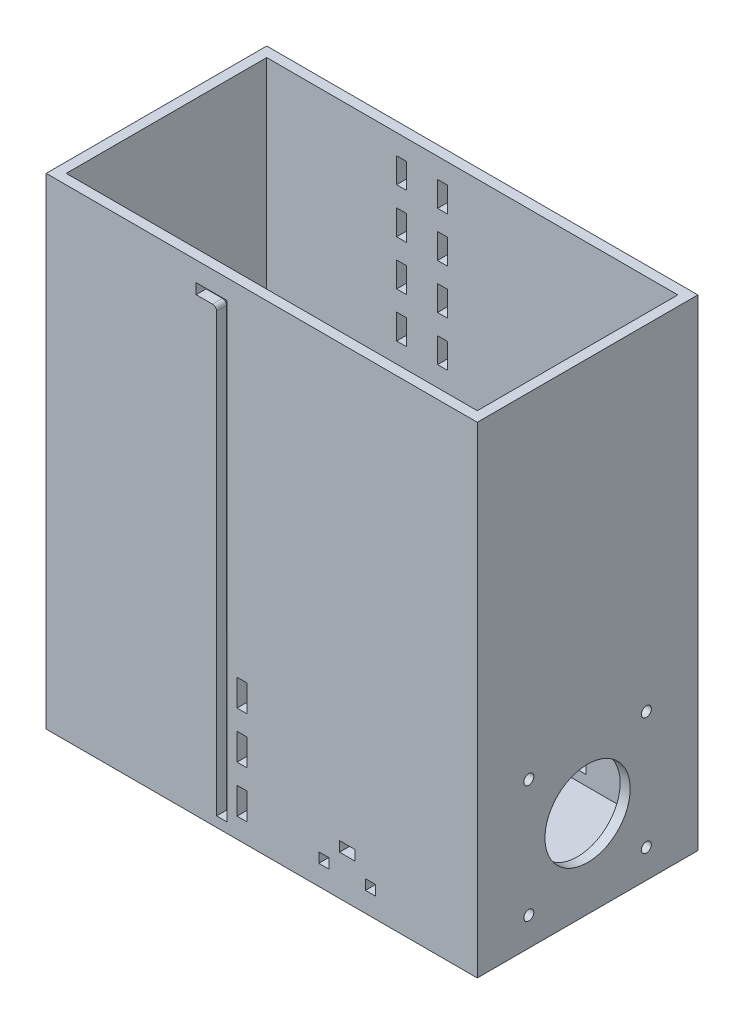
SolidWorks part; units mm, degrees
material "Acrylic (Medium-high impact)"
ref_plane "Front Plane" through (0, 0, 0) normal (0, 0, 1) x (1, 0, 0)
ref_plane "Top Plane" through (0, 0, 0) normal (0, 1, 0) x (1, 0, 0)
ref_plane "Right Plane" through (0, 0, 0) normal (1, 0, 0) x (0, 0, -1)
sketch "Sketch1" plane through (0, 0, 0) normal (0, 1, 0) x (1, 0, 0)
  line L1 (-136.525, 69.85) -> (136.525, 69.85)
  line L2 (-136.525, 69.85) -> (-136.525, -69.85)
  line L3 (-136.525, -69.85) -> (136.525, -69.85)
  line L4 (136.525, 69.85) -> (136.525, -69.85)
  point P4 (-136.525, 0)
  point P6 (0, 69.85)
  dimension "D1" = 139.7
  dimension "D2" = 273.05
extrude "Boss-Extrude1" add sketch "Sketch1" along normal blind 6.35
sketch "Sketch2" plane through (0, 6.35, 0) normal (0, 1, 0) x (1, 0, 0)
  line L0 (136.525, -69.85) -> (136.525, 69.85) construction
  line L1 (-136.525, 69.85) -> (136.525, 69.85)
  line L2 (-136.525, 69.85) -> (-136.525, -69.85)
  line L3 (-136.525, -69.85) -> (136.525, -69.85)
  line L4 (136.525, 69.85) -> (136.525, -69.85)
  line L5 (-136.525, -69.85) -> (136.525, -69.85) construction
  line L7 (-130.175, 63.5) -> (130.175, 63.5)
  line L8 (-130.175, 63.5) -> (-130.175, -63.5)
  line L9 (-130.175, -63.5) -> (130.175, -63.5)
  line L10 (130.175, 63.5) -> (130.175, -63.5)
  point P7 (-130.175, 0)
  point P14 (-136.525, 0)
  point P15 (0, -63.5)
  point P16 (0, -69.85)
  point P17 (130.175, 0)
  point P18 (136.525, 0)
  dimension "D1" = 6.35
  dimension "D2" = 6.35
extrude "Boss-Extrude2" add sketch "Sketch2" along normal blind 298.45
sketch "Sketch3" plane through (0, 0, 69.85) normal (0, 0, 1) x (1, 0, 0)
  line L0 (-25.273, 304.8) -> (-25.273, 0) construction
  line L2 (-130.175, 6.35) -> (130.175, 6.35) construction
  line L4 (-28.575, 283.21) -> (-28.575, 6.35)
  line L5 (-28.575, 6.35) -> (-21.971, 6.35)
  line L6 (-21.971, 292.354) -> (-21.971, 6.35)
  line L7 (-21.971, 292.354) -> (-41.529, 292.354)
  line L9 (-31.115, 285.75) -> (-41.529, 285.75)
  line L10 (-41.529, 292.354) -> (-41.529, 285.75)
  line L11 (-21.971, 101.6) -> (-9.271, 101.6) construction
  line L12 (-136.525, 0) -> (136.525, 0) construction
  line L13 (-12.446, 88.9) -> (-12.446, 101.6) construction
  line L14 (-15.621, 88.9) -> (-9.271, 88.9)
  line L15 (-15.621, 88.9) -> (-15.621, 71.9667)
  line L16 (-15.621, 71.9667) -> (-9.271, 71.9667)
  line L17 (-9.271, 88.9) -> (-9.271, 71.9667)
  line L18 (-15.621, 42.3333) -> (-9.271, 42.3333)
  line L19 (-15.621, 42.3333) -> (-15.621, 59.2667)
  line L20 (-15.621, 59.2667) -> (-9.271, 59.2667)
  line L21 (-9.271, 42.3333) -> (-9.271, 59.2667)
  line L26 (-15.621, 29.6333) -> (-9.271, 29.6333)
  line L27 (-15.621, 29.6333) -> (-15.621, 12.7)
  line L28 (-15.621, 12.7) -> (-9.271, 12.7)
  line L29 (-9.271, 29.6333) -> (-9.271, 12.7)
  line L30 (-12.446, 59.2667) -> (-12.446, 71.9667) construction
  line L31 (-12.446, 29.6333) -> (-12.446, 42.3333) construction
  line L32 (-12.446, 12.7) -> (-12.446, 0) construction
  line L33 (-136.525, 304.8) -> (136.525, 304.8) construction
  line L34 (-130.175, 304.8) -> (-130.175, 6.35) construction
  arc A0 (-28.575, 283.21) -> (-31.115, 285.75) centre (-31.115, 283.21) ccw
  point P2 (-65.1597, 304.8)
  point P5 (-25.273, 6.35)
  point P40 (0, 0)
  point P41 (0, 0)
  point P42 (0, 0)
  point P44 (-65.2242, 0)
  point P45 (-69.6985, 0)
  dimension "D5" = 2.54
  dimension "D1" = 6.604
  dimension "D2" = 12.954
  dimension "D3" = 6.604
  dimension "D4" = 286.004
  dimension "D6" = 101.6
  dimension "D7" = 12.7
  dimension "D8" = 12.7
  dimension "D9" = 6.35
  dimension "D10" = 101.6
extrude "Door Slot" cut sketch "Sketch3" against normal blind 12.7
sketch "Sketch4" plane through (0, 0, -63.5) normal (0, 0, 1) x (1, 0, 0)
  line L0 (-136.525, 304.8) -> (136.525, 304.8) construction
  line L1 (-47.879, 304.8) -> (-41.529, 304.8)
  line L2 (-47.879, 304.8) -> (-47.879, 6.35)
  line L3 (-47.879, 6.35) -> (-41.529, 6.35)
  line L4 (-41.529, 304.8) -> (-41.529, 6.35)
  line L5 (-18.796, 263.525) -> (-18.796, 247.65) construction
  line L6 (-41.529, 292.354) -> (-41.529, 285.75) construction
  line L7 (-21.971, 304.8) -> (-15.621, 304.8)
  line L8 (-21.971, 304.8) -> (-21.971, 6.35)
  line L9 (-21.971, 6.35) -> (-15.621, 6.35)
  line L10 (-15.621, 304.8) -> (-15.621, 6.35)
  line L11 (130.175, 6.35) -> (-130.175, 6.35) construction
  line L12 (-21.971, 6.35) -> (-21.971, 292.354) construction
  line L13 (-41.529, 304.8) -> (-47.879, 304.8)
  line L14 (-41.529, 304.8) -> (-41.529, 292.1)
  line L15 (-41.529, 292.1) -> (-47.879, 292.1)
  line L16 (-47.879, 304.8) -> (-47.879, 292.1)
  line L17 (-41.529, 276.225) -> (-47.879, 276.225)
  line L18 (-41.529, 276.225) -> (-41.529, 263.525)
  line L19 (-41.529, 263.525) -> (-47.879, 263.525)
  line L20 (-47.879, 276.225) -> (-47.879, 263.525)
  line L21 (-47.879, 6.35) -> (-41.529, 6.35)
  line L22 (-47.879, 6.35) -> (-47.879, 19.05)
  line L23 (-47.879, 19.05) -> (-41.529, 19.05)
  line L24 (-41.529, 6.35) -> (-41.529, 19.05)
  line L25 (-47.879, 34.925) -> (-41.529, 34.925)
  line L26 (-47.879, 34.925) -> (-47.879, 47.625)
  line L27 (-47.879, 47.625) -> (-41.529, 47.625)
  line L28 (-41.529, 34.925) -> (-41.529, 47.625)
  line L29 (-47.879, 92.075) -> (-41.529, 92.075)
  line L30 (-47.879, 92.075) -> (-47.879, 104.775)
  line L31 (-47.879, 104.775) -> (-41.529, 104.775)
  line L32 (-41.529, 92.075) -> (-41.529, 104.775)
  line L33 (-47.879, 149.225) -> (-41.529, 149.225)
  line L34 (-47.879, 149.225) -> (-47.879, 161.925)
  line L35 (-47.879, 161.925) -> (-41.529, 161.925)
  line L36 (-41.529, 149.225) -> (-41.529, 161.925)
  line L37 (-47.879, 177.8) -> (-41.529, 177.8)
  line L38 (-47.879, 177.8) -> (-47.879, 190.5)
  line L39 (-47.879, 190.5) -> (-41.529, 190.5)
  line L40 (-41.529, 177.8) -> (-41.529, 190.5)
  line L41 (-47.879, 206.375) -> (-41.529, 206.375)
  line L42 (-47.879, 206.375) -> (-47.879, 219.075)
  line L43 (-47.879, 219.075) -> (-41.529, 219.075)
  line L44 (-41.529, 206.375) -> (-41.529, 219.075)
  line L45 (-47.879, 234.95) -> (-41.529, 234.95)
  line L46 (-47.879, 234.95) -> (-47.879, 247.65)
  line L47 (-47.879, 247.65) -> (-41.529, 247.65)
  line L48 (-41.529, 234.95) -> (-41.529, 247.65)
  line L49 (-41.529, 133.35) -> (-47.879, 133.35)
  line L50 (-41.529, 133.35) -> (-41.529, 120.65)
  line L51 (-41.529, 120.65) -> (-47.879, 120.65)
  line L52 (-47.879, 133.35) -> (-47.879, 120.65)
  line L53 (-41.529, 76.2) -> (-47.879, 76.2)
  line L54 (-41.529, 76.2) -> (-41.529, 63.5)
  line L55 (-41.529, 63.5) -> (-47.879, 63.5)
  line L56 (-47.879, 76.2) -> (-47.879, 63.5)
  line L57 (-44.704, 304.8) -> (-44.704, 292.1) construction
  line L58 (-44.704, 292.1) -> (-44.704, 276.225) construction
  line L59 (-44.704, 276.225) -> (-44.704, 263.525) construction
  line L60 (-44.704, 247.65) -> (-44.704, 234.95) construction
  line L61 (-44.704, 234.95) -> (-44.704, 219.075) construction
  line L62 (-44.704, 219.075) -> (-44.704, 206.375) construction
  line L63 (-44.704, 206.375) -> (-44.704, 190.5) construction
  line L64 (-44.704, 190.5) -> (-44.704, 177.8) construction
  line L65 (-44.704, 177.8) -> (-44.704, 161.925) construction
  line L66 (-44.704, 161.925) -> (-44.704, 149.225) construction
  line L67 (-44.704, 133.35) -> (-44.704, 120.65) construction
  line L68 (-44.704, 120.65) -> (-44.704, 104.775) construction
  line L69 (-44.704, 104.775) -> (-44.704, 92.075) construction
  line L70 (-44.704, 92.075) -> (-44.704, 76.2) construction
  line L71 (-44.704, 76.2) -> (-44.704, 63.5) construction
  line L72 (-44.704, 63.5) -> (-44.704, 47.625) construction
  line L73 (-44.704, 47.625) -> (-44.704, 34.925) construction
  line L74 (-44.704, 34.925) -> (-44.704, 19.05) construction
  line L75 (-44.704, 19.05) -> (-44.704, 6.35) construction
  line L76 (-44.704, 149.225) -> (-44.704, 133.35) construction
  line L77 (-44.704, 263.525) -> (-44.704, 247.65) construction
  line L78 (-31.75, 304.8) -> (-31.75, 0) construction
  line L79 (136.525, 304.8) -> (-136.525, 304.8) construction
  line L80 (136.525, 0) -> (-136.525, 0) construction
  line L81 (-31.75, 8.3493) -> (-21.971, 8.3493) construction
  line L82 (-31.75, 8.3493) -> (-41.529, 8.3493) construction
  line L83 (-18.796, 149.225) -> (-18.796, 133.35) construction
  line L84 (-18.796, 19.05) -> (-18.796, 6.35) construction
  line L85 (-18.796, 34.925) -> (-18.796, 19.05) construction
  line L86 (-18.796, 47.625) -> (-18.796, 34.925) construction
  line L87 (-18.796, 63.5) -> (-18.796, 47.625) construction
  line L88 (-18.796, 76.2) -> (-18.796, 63.5) construction
  line L89 (-18.796, 92.075) -> (-18.796, 76.2) construction
  line L90 (-18.796, 104.775) -> (-18.796, 92.075) construction
  line L91 (-18.796, 120.65) -> (-18.796, 104.775) construction
  line L92 (-18.796, 133.35) -> (-18.796, 120.65) construction
  line L93 (-18.796, 161.925) -> (-18.796, 149.225) construction
  line L94 (-18.796, 177.8) -> (-18.796, 161.925) construction
  line L95 (-18.796, 190.5) -> (-18.796, 177.8) construction
  line L96 (-18.796, 206.375) -> (-18.796, 190.5) construction
  line L97 (-18.796, 219.075) -> (-18.796, 206.375) construction
  line L98 (-18.796, 234.95) -> (-18.796, 219.075) construction
  line L99 (-18.796, 247.65) -> (-18.796, 234.95) construction
  line L100 (-18.796, 276.225) -> (-18.796, 263.525) construction
  line L101 (-18.796, 292.1) -> (-18.796, 276.225) construction
  line L102 (-18.796, 304.8) -> (-18.796, 292.1) construction
  line L103 (-15.621, 76.2) -> (-15.621, 63.5)
  line L104 (-21.971, 63.5) -> (-15.621, 63.5)
  line L105 (-21.971, 76.2) -> (-21.971, 63.5)
  line L106 (-21.971, 76.2) -> (-15.621, 76.2)
  line L107 (-15.621, 133.35) -> (-15.621, 120.65)
  line L108 (-21.971, 120.65) -> (-15.621, 120.65)
  line L109 (-21.971, 133.35) -> (-21.971, 120.65)
  line L110 (-21.971, 133.35) -> (-15.621, 133.35)
  line L111 (-21.971, 234.95) -> (-21.971, 247.65)
  line L112 (-15.621, 247.65) -> (-21.971, 247.65)
  line L113 (-15.621, 234.95) -> (-15.621, 247.65)
  line L114 (-15.621, 234.95) -> (-21.971, 234.95)
  line L115 (-21.971, 206.375) -> (-21.971, 219.075)
  line L116 (-15.621, 219.075) -> (-21.971, 219.075)
  line L117 (-15.621, 206.375) -> (-15.621, 219.075)
  line L118 (-15.621, 206.375) -> (-21.971, 206.375)
  line L119 (-21.971, 177.8) -> (-21.971, 190.5)
  line L120 (-15.621, 190.5) -> (-21.971, 190.5)
  line L121 (-15.621, 177.8) -> (-15.621, 190.5)
  line L122 (-15.621, 177.8) -> (-21.971, 177.8)
  line L123 (-21.971, 149.225) -> (-21.971, 161.925)
  line L124 (-15.621, 161.925) -> (-21.971, 161.925)
  line L125 (-15.621, 149.225) -> (-15.621, 161.925)
  line L126 (-15.621, 149.225) -> (-21.971, 149.225)
  line L127 (-21.971, 92.075) -> (-21.971, 104.775)
  line L128 (-15.621, 104.775) -> (-21.971, 104.775)
  line L129 (-15.621, 92.075) -> (-15.621, 104.775)
  line L130 (-15.621, 92.075) -> (-21.971, 92.075)
  line L131 (-21.971, 34.925) -> (-21.971, 47.625)
  line L132 (-15.621, 47.625) -> (-21.971, 47.625)
  line L133 (-15.621, 34.925) -> (-15.621, 47.625)
  line L134 (-15.621, 34.925) -> (-21.971, 34.925)
  line L135 (-21.971, 6.35) -> (-21.971, 19.05)
  line L136 (-15.621, 19.05) -> (-21.971, 19.05)
  line L137 (-15.621, 6.35) -> (-15.621, 19.05)
  line L138 (-15.621, 6.35) -> (-21.971, 6.35)
  line L139 (-15.621, 276.225) -> (-15.621, 263.525)
  line L140 (-21.971, 263.525) -> (-15.621, 263.525)
  line L141 (-21.971, 276.225) -> (-21.971, 263.525)
  line L142 (-21.971, 276.225) -> (-15.621, 276.225)
  line L143 (-15.621, 304.8) -> (-15.621, 292.1)
  line L144 (-21.971, 292.1) -> (-15.621, 292.1)
  line L145 (-21.971, 304.8) -> (-21.971, 292.1)
  line L146 (-21.971, 304.8) -> (-15.621, 304.8)
  line L147 (-21.971, 304.8) -> (-21.971, 6.35)
  line L148 (-15.621, 6.35) -> (-21.971, 6.35)
  line L149 (-15.621, 304.8) -> (-15.621, 6.35)
  line L150 (-15.621, 304.8) -> (-21.971, 304.8)
  point P14 (-41.529, 289.052)
  dimension "D1" = 6.35
  dimension "D2" = 12.7
extrude "Door Guide Holes" cut sketch "Sketch4" against normal up to next contours L17 L4 L15 L2 | L2 L47 L4 L19 | L45 L2 L43 L4 | L41 L2 L39 L4 | L37 L2 L35 L4 | L49 L4 L33 L2 | L4 L51 L2 L31 | L53 L4 L29 L2 | L4 L55 L2 L27 | L25 L2 L23 L4
ref_plane "Plane1" through (-31.75, 0, 0) normal (-1, 0, 0) x (0, 0, 1)
mirror "Mirror1" about plane through (-31.75, 0, 0) normal (-1, 0, 0) of "Door Guide Holes"
sketch "Lever Holes" plane through (0, 0, 69.85) normal (0, 0, 1) x (1, 0, 0)
  line L0 (49.276, 31.75) -> (58.928, 31.75)
  line L1 (49.276, 31.75) -> (49.276, 25.4)
  line L2 (49.276, 25.4) -> (58.928, 25.4)
  line L3 (58.928, 31.75) -> (58.928, 25.4)
  line L4 (36.1315, 19.05) -> (42.4815, 19.05)
  line L5 (36.1315, 19.05) -> (36.1315, 12.7)
  line L6 (36.1315, 12.7) -> (42.4815, 12.7)
  line L7 (42.4815, 19.05) -> (42.4815, 12.7)
  line L8 (65.7225, 19.05) -> (72.0725, 19.05)
  line L9 (65.7225, 19.05) -> (65.7225, 12.7)
  line L10 (65.7225, 12.7) -> (72.0725, 12.7)
  line L11 (72.0725, 19.05) -> (72.0725, 12.7)
  line L12 (42.4815, 15.875) -> (65.7225, 15.875) construction
  line L13 (-136.525, 0) -> (136.525, 0) construction
  line L14 (-21.971, 6.35) -> (130.175, 6.35) construction
  line L15 (130.175, 6.35) -> (-130.175, 6.35) construction
  point P12 (54.102, 15.875)
  point P13 (54.102, 25.4)
  point P14 (39.3065, 12.7)
  point P24 (54.102, 6.35)
  point P25 (0, 0)
  dimension "D1" = 9.652
  dimension "D2" = 6.35
  dimension "D3" = 6.35
  dimension "D4" = 6.35
  dimension "D5" = 23.241
  dimension "D6" = 25.4
  dimension "D7" = 12.7
extrude "Cut-Extrude1" cut sketch "Lever Holes" against normal through all
sketch "Sketch7" plane through (136.525, 0, 0) normal (1, 0, 0) x (0, 0, -1)
  line L0 (-37.211, 92.583) -> (37.211, 92.583)
  line L1 (-37.211, 92.583) -> (-37.211, 18.161)
  line L2 (-37.211, 18.161) -> (37.211, 18.161)
  line L3 (37.211, 92.583) -> (37.211, 18.161)
  line L4 (-69.85, 0) -> (69.85, 0) construction
  circle A0 centre (0, 55.372) radius 26.9875
  circle A1 centre (-37.211, 92.583) radius 3.175
  circle A2 centre (37.211, 92.583) radius 3.175
  circle A3 centre (-37.211, 18.161) radius 3.175
  circle A4 centre (37.211, 18.161) radius 3.175
  point P9 (0, 18.161)
  point P10 (-37.211, 55.372)
  point P12 (43.7877, 25.7461)
  point P15 (0, 0)
  dimension "D3" = 53.975
  dimension "D4" = 6.35
  dimension "D1" = 74.422
  dimension "D2" = 55.372
extrude "Cut-Extrude2" cut sketch "Sketch7" against normal up to next contours A0 | L0 A1 L1 | L1 A1 L0 | L3 A2 L0 | L0 A2 L3 | L2 A3 L1 | L1 A3 L2 | L2 A4 L3 | L3 A4 L2
sketch "Sketch8" plane through (-136.525, 0, 0) normal (-1, 0, 0) x (0, 0, 1)
  line L0 (-69.85, 0) -> (69.85, 0) construction
  circle A0 centre (0, 19.05) radius 3.175
  point P2 (0, 0)
  point P6 (0, 0)
  dimension "D1" = 6.35
  dimension "D2" = 19.05
extrude "Cut-Extrude3" cut sketch "Sketch8" against normal up to next
sketch "Bottom" plane through (0, 0, 0) normal (0, -1, 0) x (1, 0, 0)
  line L0 (-130.175, 63.5) -> (130.175, 63.5) construction
  line L1 (-136.525, 69.85) -> (-122.1539, 69.85)
  line L2 (-136.525, 69.85) -> (-136.525, 63.5)
  line L3 (-136.525, 63.5) -> (-122.1539, 63.5)
  line L4 (-122.1539, 69.85) -> (-122.1539, 63.5)
  line L5 (-122.1539, 69.85) -> (-107.7829, 69.85)
  line L6 (-122.1539, 69.85) -> (-122.1539, 63.5)
  line L7 (-122.1539, 63.5) -> (-107.7829, 63.5)
  line L8 (-107.7829, 69.85) -> (-107.7829, 63.5)
  line L9 (-107.7829, 69.85) -> (-93.4118, 69.85)
  line L10 (-107.7829, 69.85) -> (-107.7829, 63.5)
  line L11 (-107.7829, 63.5) -> (-93.4118, 63.5)
  line L12 (-93.4118, 69.85) -> (-93.4118, 63.5)
  line L13 (-93.4118, 69.85) -> (-79.0408, 69.85)
  line L14 (-93.4118, 69.85) -> (-93.4118, 63.5)
  line L15 (-93.4118, 63.5) -> (-79.0408, 63.5)
  line L16 (-79.0408, 69.85) -> (-79.0408, 63.5)
  line L17 (-136.525, 69.85) -> (136.525, 69.85) construction
  line L18 (-41.529, 63.5) -> (-21.971, 63.5) construction
  line L19 (-79.0408, 69.85) -> (-64.6697, 69.85)
  line L20 (-79.0408, 69.85) -> (-79.0408, 63.5)
  line L21 (-79.0408, 63.5) -> (-64.6697, 63.5)
  line L22 (-64.6697, 69.85) -> (-64.6697, 63.5)
  line L23 (-64.6697, 69.85) -> (-50.2987, 69.85)
  line L24 (-64.6697, 69.85) -> (-64.6697, 63.5)
  line L25 (-64.6697, 63.5) -> (-50.2987, 63.5)
  line L26 (-50.2987, 69.85) -> (-50.2987, 63.5)
  line L27 (-50.2987, 69.85) -> (-35.9276, 69.85)
  line L28 (-50.2987, 69.85) -> (-50.2987, 63.5)
  line L29 (-50.2987, 63.5) -> (-35.9276, 63.5)
  line L30 (-35.9276, 69.85) -> (-35.9276, 63.5)
  line L31 (-35.9276, 69.85) -> (-21.5566, 69.85)
  line L32 (-35.9276, 69.85) -> (-35.9276, 63.5)
  line L33 (-35.9276, 63.5) -> (-21.5566, 63.5)
  line L34 (-21.5566, 69.85) -> (-21.5566, 63.5)
  line L36 (-21.5566, 69.85) -> (-7.1855, 69.85)
  line L37 (-21.5566, 69.85) -> (-21.5566, 63.5)
  line L38 (-21.5566, 63.5) -> (-7.1855, 63.5)
  line L39 (-7.1855, 69.85) -> (-7.1855, 63.5)
  line L40 (-7.1855, 69.85) -> (7.1855, 69.85)
  line L41 (-7.1855, 69.85) -> (-7.1855, 63.5)
  line L42 (-7.1855, 63.5) -> (7.1855, 63.5)
  line L43 (7.1855, 69.85) -> (7.1855, 63.5)
  line L44 (7.1855, 69.85) -> (21.5566, 69.85)
  line L45 (7.1855, 69.85) -> (7.1855, 63.5)
  line L46 (7.1855, 63.5) -> (21.5566, 63.5)
  line L47 (21.5566, 69.85) -> (21.5566, 63.5)
  line L48 (21.5566, 69.85) -> (35.9276, 69.85)
  line L49 (21.5566, 69.85) -> (21.5566, 63.5)
  line L50 (21.5566, 63.5) -> (35.9276, 63.5)
  line L51 (35.9276, 69.85) -> (35.9276, 63.5)
  line L52 (35.9276, 69.85) -> (50.2987, 69.85)
  line L53 (35.9276, 69.85) -> (35.9276, 63.5)
  line L54 (35.9276, 63.5) -> (50.2987, 63.5)
  line L55 (50.2987, 69.85) -> (50.2987, 63.5)
  line L56 (50.2987, 69.85) -> (64.6697, 69.85)
  line L57 (50.2987, 69.85) -> (50.2987, 63.5)
  line L58 (50.2987, 63.5) -> (64.6697, 63.5)
  line L59 (64.6697, 69.85) -> (64.6697, 63.5)
  line L60 (64.6697, 69.85) -> (79.0408, 69.85)
  line L61 (64.6697, 69.85) -> (64.6697, 63.5)
  line L62 (64.6697, 63.5) -> (79.0408, 63.5)
  line L63 (79.0408, 69.85) -> (79.0408, 63.5)
  line L64 (79.0408, 69.85) -> (93.4118, 69.85)
  line L65 (79.0408, 69.85) -> (79.0408, 63.5)
  line L66 (79.0408, 63.5) -> (93.4118, 63.5)
  line L67 (93.4118, 69.85) -> (93.4118, 63.5)
  line L68 (93.4118, 69.85) -> (107.7829, 69.85)
  line L69 (93.4118, 69.85) -> (93.4118, 63.5)
  line L70 (93.4118, 63.5) -> (107.7829, 63.5)
  line L71 (107.7829, 69.85) -> (107.7829, 63.5)
  line L72 (107.7829, 69.85) -> (122.1539, 69.85)
  line L73 (107.7829, 69.85) -> (107.7829, 63.5)
  line L74 (107.7829, 63.5) -> (122.1539, 63.5)
  line L75 (122.1539, 69.85) -> (122.1539, 63.5)
  line L76 (-130.175, -63.5) -> (-130.175, 63.5) construction
  line L77 (-136.525, 69.85) -> (-130.175, 69.85)
  line L78 (-136.525, 69.85) -> (-136.525, 57.15)
  line L79 (-136.525, 57.15) -> (-130.175, 57.15)
  line L80 (-130.175, 69.85) -> (-130.175, 57.15)
  line L82 (-136.525, 57.15) -> (-130.175, 57.15)
  line L83 (-136.525, 57.15) -> (-136.525, 44.45)
  line L84 (-136.525, 44.45) -> (-130.175, 44.45)
  line L85 (-130.175, 57.15) -> (-130.175, 44.45)
  line L86 (-136.525, 44.45) -> (-130.175, 44.45)
  line L87 (-136.525, 44.45) -> (-136.525, 31.75)
  line L88 (-136.525, 31.75) -> (-130.175, 31.75)
  line L89 (-130.175, 44.45) -> (-130.175, 31.75)
  line L90 (-136.525, 31.75) -> (-130.175, 31.75)
  line L91 (-136.525, 31.75) -> (-136.525, 19.05)
  line L92 (-136.525, 19.05) -> (-130.175, 19.05)
  line L93 (-130.175, 31.75) -> (-130.175, 19.05)
  line L94 (-136.525, 19.05) -> (-130.175, 19.05)
  line L95 (-136.525, 19.05) -> (-136.525, 6.35)
  line L96 (-136.525, 6.35) -> (-130.175, 6.35)
  line L97 (-130.175, 19.05) -> (-130.175, 6.35)
  line L98 (-136.525, 6.35) -> (-130.175, 6.35)
  line L99 (-136.525, 6.35) -> (-136.525, -6.35)
  line L100 (-136.525, -6.35) -> (-130.175, -6.35)
  line L101 (-130.175, 6.35) -> (-130.175, -6.35)
  line L102 (-136.525, -6.35) -> (-130.175, -6.35)
  line L103 (-136.525, -6.35) -> (-136.525, -19.05)
  line L104 (-136.525, -19.05) -> (-130.175, -19.05)
  line L105 (-130.175, -6.35) -> (-130.175, -19.05)
  line L106 (-136.525, -19.05) -> (-130.175, -19.05)
  line L107 (-136.525, -19.05) -> (-136.525, -31.75)
  line L108 (-136.525, -31.75) -> (-130.175, -31.75)
  line L109 (-130.175, -19.05) -> (-130.175, -31.75)
  line L110 (-136.525, -31.75) -> (-130.175, -31.75)
  line L111 (-136.525, -31.75) -> (-136.525, -44.45)
  line L112 (-136.525, -44.45) -> (-130.175, -44.45)
  line L113 (-130.175, -31.75) -> (-130.175, -44.45)
  line L114 (-136.525, -44.45) -> (-130.175, -44.45)
  line L115 (-136.525, -44.45) -> (-136.525, -57.15)
  line L116 (-136.525, -57.15) -> (-130.175, -57.15)
  line L117 (-130.175, -44.45) -> (-130.175, -57.15)
  line L118 (136.525, 69.85) -> (136.525, -69.85) construction
  line L119 (122.1539, 69.85) -> (136.525, 69.85)
  line L120 (122.1539, 69.85) -> (122.1539, 63.5)
  line L121 (122.1539, 63.5) -> (136.525, 63.5)
  line L122 (136.525, 69.85) -> (136.525, 63.5)
  line L123 (136.525, -69.85) -> (-136.525, -69.85) construction
  line L124 (-136.525, -57.15) -> (-130.175, -57.15)
  line L125 (-136.525, -57.15) -> (-136.525, -69.85)
  line L126 (-136.525, -69.85) -> (-130.175, -69.85)
  line L127 (-130.175, -57.15) -> (-130.175, -69.85)
  line L128 (150.1775, 0) -> (-150.1775, 0) construction
  line L129 (136.525, -69.85) -> (136.525, -63.5)
  line L130 (122.1539, -63.5) -> (136.525, -63.5)
  line L131 (122.1539, -69.85) -> (136.525, -69.85)
  line L132 (122.1539, -69.85) -> (122.1539, -63.5)
  line L133 (107.7829, -63.5) -> (122.1539, -63.5)
  line L134 (107.7829, -69.85) -> (122.1539, -69.85)
  line L135 (107.7829, -69.85) -> (107.7829, -63.5)
  line L136 (93.4118, -63.5) -> (107.7829, -63.5)
  line L137 (93.4118, -69.85) -> (107.7829, -69.85)
  line L138 (93.4118, -69.85) -> (93.4118, -63.5)
  line L139 (79.0408, -63.5) -> (93.4118, -63.5)
  line L140 (79.0408, -69.85) -> (93.4118, -69.85)
  line L141 (79.0408, -69.85) -> (79.0408, -63.5)
  line L142 (64.6697, -63.5) -> (79.0408, -63.5)
  line L143 (64.6697, -69.85) -> (79.0408, -69.85)
  line L144 (50.2987, -63.5) -> (64.6697, -63.5)
  line L145 (64.6697, -69.85) -> (64.6697, -63.5)
  line L146 (50.2987, -69.85) -> (64.6697, -69.85)
  line L147 (50.2987, -69.85) -> (50.2987, -63.5)
  line L148 (35.9276, -63.5) -> (50.2987, -63.5)
  line L149 (35.9276, -69.85) -> (50.2987, -69.85)
  line L150 (35.9276, -69.85) -> (35.9276, -63.5)
  line L151 (21.5566, -63.5) -> (35.9276, -63.5)
  line L152 (21.5566, -69.85) -> (35.9276, -69.85)
  line L153 (21.5566, -69.85) -> (21.5566, -63.5)
  line L154 (7.1855, -69.85) -> (21.5566, -69.85)
  line L155 (7.1855, -63.5) -> (21.5566, -63.5)
  line L156 (7.1855, -69.85) -> (7.1855, -63.5)
  line L157 (-7.1855, -63.5) -> (7.1855, -63.5)
  line L158 (-7.1855, -69.85) -> (7.1855, -69.85)
  line L159 (-21.5566, -63.5) -> (-7.1855, -63.5)
  line L160 (-7.1855, -69.85) -> (-7.1855, -63.5)
  line L161 (-21.5566, -69.85) -> (-7.1855, -69.85)
  line L162 (-21.5566, -69.85) -> (-21.5566, -63.5)
  line L163 (-35.9276, -63.5) -> (-21.5566, -63.5)
  line L164 (-35.9276, -69.85) -> (-21.5566, -69.85)
  line L165 (-35.9276, -69.85) -> (-35.9276, -63.5)
  line L166 (-50.2987, -63.5) -> (-35.9276, -63.5)
  line L167 (-50.2987, -69.85) -> (-35.9276, -69.85)
  line L168 (-50.2987, -69.85) -> (-50.2987, -63.5)
  line L169 (-64.6697, -69.85) -> (-50.2987, -69.85)
  line L170 (-64.6697, -63.5) -> (-50.2987, -63.5)
  line L171 (-79.0408, -63.5) -> (-64.6697, -63.5)
  line L172 (-64.6697, -69.85) -> (-64.6697, -63.5)
  line L173 (-79.0408, -69.85) -> (-64.6697, -69.85)
  line L174 (-93.4118, -69.85) -> (-79.0408, -69.85)
  line L175 (-93.4118, -63.5) -> (-79.0408, -63.5)
  line L176 (-79.0408, -69.85) -> (-79.0408, -63.5)
  line L177 (-107.7829, -69.85) -> (-107.7829, -63.5)
  line L178 (-107.7829, -69.85) -> (-93.4118, -69.85)
  line L179 (-93.4118, -69.85) -> (-93.4118, -63.5)
  line L180 (-107.7829, -63.5) -> (-93.4118, -63.5)
  line L181 (-122.1539, -63.5) -> (-107.7829, -63.5)
  line L182 (-122.1539, -69.85) -> (-107.7829, -69.85)
  line L183 (-122.1539, -69.85) -> (-122.1539, -63.5)
  line L184 (-136.525, -69.85) -> (-122.1539, -69.85)
  line L185 (-136.525, -69.85) -> (-136.525, -63.5)
  line L186 (-136.525, -63.5) -> (-122.1539, -63.5)
  line L187 (0, -76.835) -> (0, 76.835) construction
  line L188 (136.525, -69.85) -> (130.175, -69.85)
  line L189 (130.175, -57.15) -> (130.175, -69.85)
  line L190 (136.525, -57.15) -> (136.525, -69.85)
  line L191 (136.525, -57.15) -> (130.175, -57.15)
  line L192 (130.175, -44.45) -> (130.175, -57.15)
  line L193 (136.525, -44.45) -> (136.525, -57.15)
  line L194 (136.525, -44.45) -> (130.175, -44.45)
  line L195 (130.175, -31.75) -> (130.175, -44.45)
  line L196 (136.525, -31.75) -> (136.525, -44.45)
  line L197 (136.525, -31.75) -> (130.175, -31.75)
  line L198 (136.525, -19.05) -> (136.525, -31.75)
  line L199 (130.175, -19.05) -> (130.175, -31.75)
  line L200 (130.175, -6.35) -> (130.175, -19.05)
  line L201 (136.525, -6.35) -> (136.525, -19.05)
  line L202 (136.525, -19.05) -> (130.175, -19.05)
  line L203 (136.525, -6.35) -> (130.175, -6.35)
  line L204 (130.175, 6.35) -> (130.175, -6.35)
  line L205 (136.525, 6.35) -> (136.525, -6.35)
  line L206 (136.525, 6.35) -> (130.175, 6.35)
  line L207 (130.175, 19.05) -> (130.175, 6.35)
  line L208 (136.525, 19.05) -> (136.525, 6.35)
  line L209 (136.525, 19.05) -> (130.175, 19.05)
  line L210 (136.525, 31.75) -> (130.175, 31.75)
  line L211 (136.525, 44.45) -> (130.175, 44.45)
  line L212 (136.525, 57.15) -> (130.175, 57.15)
  line L213 (130.175, 31.75) -> (130.175, 19.05)
  line L214 (136.525, 31.75) -> (136.525, 19.05)
  line L215 (130.175, 44.45) -> (130.175, 31.75)
  line L216 (136.525, 44.45) -> (136.525, 31.75)
  line L217 (130.175, 57.15) -> (130.175, 44.45)
  line L218 (136.525, 57.15) -> (136.525, 44.45)
  line L219 (130.175, 69.85) -> (130.175, 57.15)
  line L220 (136.525, 69.85) -> (136.525, 57.15)
sketch "Front/Back" plane through (0, 0, 69.85) normal (0, 0, 1) x (1, 0, 0)
  line L0 (-130.175, 6.35) -> (-28.575, 6.35) construction
  line L1 (-136.525, 0) -> (-122.1539, 0)
  line L2 (-136.525, 0) -> (-136.525, 6.35)
  line L3 (-136.525, 6.35) -> (-122.1539, 6.35)
  line L4 (-122.1539, 0) -> (-122.1539, 6.35)
  line L5 (-136.525, 0) -> (136.525, 0) construction
  line L6 (-107.7829, 0) -> (-93.4118, 0) construction
  line L7 (-122.1539, 6.35) -> (-107.7829, 6.35)
  line L8 (-122.1539, 6.35) -> (-122.1539, 0)
  line L9 (-122.1539, 0) -> (-107.7829, 0)
  line L10 (-107.7829, 6.35) -> (-107.7829, 0)
  line L11 (-79.0408, 0) -> (-64.6697, 0) construction
  line L12 (-107.7829, 6.35) -> (-93.4118, 6.35)
  line L13 (-107.7829, 6.35) -> (-107.7829, 0)
  line L14 (-107.7829, 0) -> (-93.4118, 0)
  line L15 (-93.4118, 6.35) -> (-93.4118, 0)
  line L16 (-93.4118, 6.35) -> (-79.0408, 6.35)
  line L17 (-93.4118, 6.35) -> (-93.4118, 0)
  line L18 (-93.4118, 0) -> (-79.0408, 0)
  line L19 (-79.0408, 6.35) -> (-79.0408, 0)
  line L20 (-64.6697, 0) -> (-50.2987, 0) construction
  line L21 (-79.0408, 6.35) -> (-64.6697, 6.35)
  line L22 (-79.0408, 6.35) -> (-79.0408, 0)
  line L23 (-79.0408, 0) -> (-64.6697, 0)
  line L24 (-64.6697, 6.35) -> (-64.6697, 0)
  line L25 (-64.6697, 6.35) -> (-50.2987, 6.35)
  line L26 (-64.6697, 6.35) -> (-64.6697, 0)
  line L27 (-64.6697, 0) -> (-50.2987, 0)
  line L28 (-50.2987, 6.35) -> (-50.2987, 0)
  line L29 (-50.2987, 0) -> (-35.9276, 0) construction
  line L30 (-50.2987, 6.35) -> (-35.9276, 6.35)
  line L31 (-50.2987, 6.35) -> (-50.2987, 0)
  line L32 (-50.2987, 0) -> (-35.9276, 0)
  line L33 (-35.9276, 6.35) -> (-35.9276, 0)
  line L34 (-21.5566, 0) -> (-7.1855, 0) construction
  line L35 (-35.9276, 6.35) -> (-21.5566, 6.35)
  line L36 (-35.9276, 6.35) -> (-35.9276, 0)
  line L37 (-35.9276, 0) -> (-21.5566, 0)
  line L38 (-21.5566, 6.35) -> (-21.5566, 0)
  line L39 (7.1855, 0) -> (21.5566, 0) construction
  line L40 (-21.5566, 6.35) -> (-7.1855, 6.35)
  line L41 (-21.5566, 6.35) -> (-21.5566, 0)
  line L42 (-21.5566, 0) -> (-7.1855, 0)
  line L43 (-7.1855, 6.35) -> (-7.1855, 0)
  line L44 (-7.1855, 6.35) -> (7.1855, 6.35)
  line L45 (-7.1855, 6.35) -> (-7.1855, 0)
  line L46 (-7.1855, 0) -> (7.1855, 0)
  line L47 (7.1855, 6.35) -> (7.1855, 0)
  line L48 (7.1855, 0) -> (21.5566, 0) construction
  line L49 (35.9276, 0) -> (50.2987, 0) construction
  line L50 (7.1855, 6.35) -> (21.5566, 6.35)
  line L51 (7.1855, 6.35) -> (7.1855, 0)
  line L52 (7.1855, 0) -> (21.5566, 0)
  line L53 (21.5566, 6.35) -> (21.5566, 0)
  line L54 (21.5566, 6.35) -> (35.9276, 6.35)
  line L55 (21.5566, 6.35) -> (21.5566, 0)
  line L56 (21.5566, 0) -> (35.9276, 0)
  line L57 (35.9276, 6.35) -> (35.9276, 0)
  line L58 (64.6697, 0) -> (79.0408, 0) construction
  line L59 (35.9276, 6.35) -> (50.2987, 6.35)
  line L60 (35.9276, 6.35) -> (35.9276, 0)
  line L61 (35.9276, 0) -> (50.2987, 0)
  line L62 (50.2987, 6.35) -> (50.2987, 0)
  line L63 (50.2987, 6.35) -> (64.6697, 6.35)
  line L64 (50.2987, 6.35) -> (50.2987, 0)
  line L65 (50.2987, 0) -> (64.6697, 0)
  line L66 (64.6697, 6.35) -> (64.6697, 0)
  line L67 (50.2987, 0) -> (64.6697, 0) construction
  line L68 (93.4118, 0) -> (107.7829, 0) construction
  line L69 (64.6697, 6.35) -> (79.0408, 6.35)
  line L70 (64.6697, 6.35) -> (64.6697, 0)
  line L71 (64.6697, 0) -> (79.0408, 0)
  line L72 (79.0408, 6.35) -> (79.0408, 0)
  line L73 (79.0408, 6.35) -> (93.4118, 6.35)
  line L74 (79.0408, 6.35) -> (79.0408, 0)
  line L75 (79.0408, 0) -> (93.4118, 0)
  line L76 (93.4118, 6.35) -> (93.4118, 0)
  line L77 (107.7829, 0) -> (122.1539, 0) construction
  line L78 (93.4118, 6.35) -> (107.7829, 6.35)
  line L79 (93.4118, 6.35) -> (93.4118, 0)
  line L80 (93.4118, 0) -> (107.7829, 0)
  line L81 (107.7829, 6.35) -> (107.7829, 0)
  line L82 (107.7829, 0) -> (122.1539, 0) construction
  line L84 (107.7829, 6.35) -> (122.1539, 6.35)
  line L85 (107.7829, 6.35) -> (107.7829, 0)
  line L86 (107.7829, 0) -> (122.1539, 0)
  line L87 (122.1539, 6.35) -> (122.1539, 0)
  line L88 (122.1539, 6.35) -> (136.525, 6.35)
  line L89 (122.1539, 6.35) -> (122.1539, 0)
  line L90 (122.1539, 0) -> (136.525, 0)
  line L91 (136.525, 6.35) -> (136.525, 0)
  line L92 (-130.175, 304.8) -> (-130.175, 6.35) construction
  line L93 (-136.525, 0) -> (-130.175, 0)
  line L94 (-136.525, 0) -> (-136.525, 12.7)
  line L95 (-136.525, 12.7) -> (-130.175, 12.7)
  line L96 (-130.175, 0) -> (-130.175, 12.7)
  line L97 (-136.525, 304.8) -> (-136.525, 0) construction
  line L98 (-136.525, 12.7) -> (-130.175, 12.7)
  line L99 (-136.525, 12.7) -> (-136.525, 25.4)
  line L100 (-136.525, 25.4) -> (-130.175, 25.4)
  line L101 (-130.175, 12.7) -> (-130.175, 25.4)
  line L102 (-136.525, 25.4) -> (-130.175, 25.4)
  line L103 (-136.525, 25.4) -> (-136.525, 38.1)
  line L104 (-136.525, 38.1) -> (-130.175, 38.1)
  line L105 (-130.175, 25.4) -> (-130.175, 38.1)
  line L106 (-136.525, 38.1) -> (-130.175, 38.1)
  line L107 (-136.525, 38.1) -> (-136.525, 50.8)
  line L108 (-136.525, 50.8) -> (-130.175, 50.8)
  line L109 (-130.175, 38.1) -> (-130.175, 50.8)
  line L110 (-136.525, 50.8) -> (-130.175, 50.8)
  line L111 (-136.525, 50.8) -> (-136.525, 63.5)
  line L112 (-136.525, 63.5) -> (-130.175, 63.5)
  line L113 (-130.175, 50.8) -> (-130.175, 63.5)
  line L114 (-136.525, 63.5) -> (-130.175, 63.5)
  line L115 (-136.525, 63.5) -> (-136.525, 76.2)
  line L116 (-136.525, 76.2) -> (-130.175, 76.2)
  line L117 (-130.175, 63.5) -> (-130.175, 76.2)
  line L118 (-136.525, 76.2) -> (-130.175, 76.2)
  line L119 (-136.525, 76.2) -> (-136.525, 88.9)
  line L120 (-136.525, 88.9) -> (-130.175, 88.9)
  line L121 (-130.175, 76.2) -> (-130.175, 88.9)
  line L122 (-136.525, 88.9) -> (-130.175, 88.9)
  line L123 (-136.525, 88.9) -> (-136.525, 101.6)
  line L124 (-136.525, 101.6) -> (-130.175, 101.6)
  line L125 (-130.175, 88.9) -> (-130.175, 101.6)
  line L126 (-136.525, 101.6) -> (-130.175, 101.6)
  line L127 (-136.525, 101.6) -> (-136.525, 114.3)
  line L128 (-136.525, 114.3) -> (-130.175, 114.3)
  line L129 (-130.175, 101.6) -> (-130.175, 114.3)
  line L130 (-136.525, 114.3) -> (-130.175, 114.3)
  line L131 (-136.525, 114.3) -> (-136.525, 127)
  line L132 (-136.525, 127) -> (-130.175, 127)
  line L133 (-130.175, 114.3) -> (-130.175, 127)
  line L134 (-136.525, 127) -> (-130.175, 127)
  line L135 (-136.525, 127) -> (-136.525, 139.7)
  line L136 (-136.525, 139.7) -> (-130.175, 139.7)
  line L137 (-130.175, 127) -> (-130.175, 139.7)
  line L138 (-136.525, 139.7) -> (-130.175, 139.7)
  line L139 (-136.525, 139.7) -> (-136.525, 152.4)
  line L140 (-136.525, 152.4) -> (-130.175, 152.4)
  line L141 (-130.175, 139.7) -> (-130.175, 152.4)
  line L142 (-136.525, 152.4) -> (-130.175, 152.4)
  line L143 (-136.525, 152.4) -> (-136.525, 165.1)
  line L144 (-136.525, 165.1) -> (-130.175, 165.1)
  line L145 (-130.175, 152.4) -> (-130.175, 165.1)
  line L146 (-136.525, 165.1) -> (-130.175, 165.1)
  line L147 (-136.525, 165.1) -> (-136.525, 177.8)
  line L148 (-136.525, 177.8) -> (-130.175, 177.8)
  line L149 (-130.175, 165.1) -> (-130.175, 177.8)
  line L150 (-136.525, 177.8) -> (-130.175, 177.8)
  line L151 (-136.525, 177.8) -> (-136.525, 190.5)
  line L152 (-136.525, 190.5) -> (-130.175, 190.5)
  line L153 (-130.175, 177.8) -> (-130.175, 190.5)
  line L154 (-136.525, 190.5) -> (-130.175, 190.5)
  line L155 (-136.525, 190.5) -> (-136.525, 203.2)
  line L156 (-136.525, 203.2) -> (-130.175, 203.2)
  line L157 (-130.175, 190.5) -> (-130.175, 203.2)
  line L158 (-136.525, 203.2) -> (-130.175, 203.2)
  line L159 (-136.525, 203.2) -> (-136.525, 215.9)
  line L160 (-136.525, 215.9) -> (-130.175, 215.9)
  line L161 (-130.175, 203.2) -> (-130.175, 215.9)
  line L162 (-136.525, 215.9) -> (-130.175, 215.9)
  line L163 (-136.525, 215.9) -> (-136.525, 228.6)
  line L164 (-136.525, 228.6) -> (-130.175, 228.6)
  line L165 (-130.175, 215.9) -> (-130.175, 228.6)
  line L166 (-136.525, 228.6) -> (-130.175, 228.6)
  line L167 (-136.525, 228.6) -> (-136.525, 241.3)
  line L168 (-136.525, 241.3) -> (-130.175, 241.3)
  line L169 (-130.175, 228.6) -> (-130.175, 241.3)
  line L170 (-136.525, 241.3) -> (-130.175, 241.3)
  line L171 (-136.525, 241.3) -> (-136.525, 254)
  line L172 (-136.525, 254) -> (-130.175, 254)
  line L173 (-130.175, 241.3) -> (-130.175, 254)
  line L174 (-136.525, 254) -> (-130.175, 254)
  line L175 (-136.525, 254) -> (-136.525, 266.7)
  line L176 (-136.525, 266.7) -> (-130.175, 266.7)
  line L177 (-130.175, 254) -> (-130.175, 266.7)
  line L178 (-136.525, 266.7) -> (-130.175, 266.7)
  line L179 (-136.525, 266.7) -> (-136.525, 279.4)
  line L180 (-136.525, 279.4) -> (-130.175, 279.4)
  line L181 (-130.175, 266.7) -> (-130.175, 279.4)
  line L182 (-136.525, 279.4) -> (-130.175, 279.4)
  line L183 (-136.525, 279.4) -> (-136.525, 292.1)
  line L184 (-136.525, 292.1) -> (-130.175, 292.1)
  line L185 (-130.175, 279.4) -> (-130.175, 292.1)
  line L186 (-136.525, 292.1) -> (-130.175, 292.1)
  line L187 (-136.525, 292.1) -> (-136.525, 304.8)
  line L188 (-136.525, 304.8) -> (-130.175, 304.8)
  line L189 (-130.175, 292.1) -> (-130.175, 304.8)
  line L190 (-136.525, 304.8) -> (-130.175, 304.8)
  line L194 (-136.525, 304.8) -> (136.525, 304.8) construction
  line L195 (0, -76.835) -> (0, 76.835) construction
  line L196 (136.525, 304.8) -> (130.175, 304.8)
  line L197 (130.175, 292.1) -> (130.175, 304.8)
  line L198 (136.525, 304.8) -> (130.175, 304.8)
  line L199 (136.525, 292.1) -> (136.525, 304.8)
  line L200 (136.525, 292.1) -> (130.175, 292.1)
  line L201 (130.175, 279.4) -> (130.175, 292.1)
  line L202 (136.525, 292.1) -> (130.175, 292.1)
  line L203 (136.525, 279.4) -> (136.525, 292.1)
  line L204 (136.525, 279.4) -> (130.175, 279.4)
  line L205 (130.175, 266.7) -> (130.175, 279.4)
  line L206 (136.525, 279.4) -> (130.175, 279.4)
  line L207 (136.525, 266.7) -> (136.525, 279.4)
  line L208 (136.525, 266.7) -> (130.175, 266.7)
  line L209 (130.175, 254) -> (130.175, 266.7)
  line L210 (136.525, 266.7) -> (130.175, 266.7)
  line L211 (136.525, 254) -> (136.525, 266.7)
  line L212 (136.525, 254) -> (130.175, 254)
  line L213 (130.175, 241.3) -> (130.175, 254)
  line L214 (136.525, 254) -> (130.175, 254)
  line L215 (136.525, 241.3) -> (136.525, 254)
  line L216 (136.525, 241.3) -> (130.175, 241.3)
  line L217 (130.175, 228.6) -> (130.175, 241.3)
  line L218 (136.525, 241.3) -> (130.175, 241.3)
  line L219 (136.525, 228.6) -> (136.525, 241.3)
  line L220 (136.525, 228.6) -> (130.175, 228.6)
  line L221 (130.175, 215.9) -> (130.175, 228.6)
  line L222 (136.525, 228.6) -> (130.175, 228.6)
  line L223 (136.525, 215.9) -> (136.525, 228.6)
  line L224 (136.525, 215.9) -> (130.175, 215.9)
  line L225 (130.175, 203.2) -> (130.175, 215.9)
  line L226 (136.525, 215.9) -> (130.175, 215.9)
  line L227 (136.525, 203.2) -> (136.525, 215.9)
  line L228 (136.525, 203.2) -> (130.175, 203.2)
  line L229 (130.175, 190.5) -> (130.175, 203.2)
  line L230 (136.525, 203.2) -> (130.175, 203.2)
  line L231 (136.525, 190.5) -> (136.525, 203.2)
  line L232 (136.525, 190.5) -> (130.175, 190.5)
  line L233 (130.175, 177.8) -> (130.175, 190.5)
  line L234 (136.525, 190.5) -> (130.175, 190.5)
  line L235 (136.525, 177.8) -> (136.525, 190.5)
  line L236 (136.525, 177.8) -> (130.175, 177.8)
  line L237 (130.175, 165.1) -> (130.175, 177.8)
  line L238 (136.525, 177.8) -> (130.175, 177.8)
  line L239 (136.525, 165.1) -> (136.525, 177.8)
  line L240 (136.525, 165.1) -> (130.175, 165.1)
  line L241 (130.175, 152.4) -> (130.175, 165.1)
  line L242 (136.525, 165.1) -> (130.175, 165.1)
  line L243 (136.525, 152.4) -> (136.525, 165.1)
  line L244 (136.525, 152.4) -> (130.175, 152.4)
  line L245 (130.175, 139.7) -> (130.175, 152.4)
  line L246 (136.525, 152.4) -> (130.175, 152.4)
  line L247 (136.525, 139.7) -> (136.525, 152.4)
  line L248 (136.525, 139.7) -> (130.175, 139.7)
  line L249 (130.175, 127) -> (130.175, 139.7)
  line L250 (136.525, 139.7) -> (130.175, 139.7)
  line L251 (136.525, 127) -> (136.525, 139.7)
  line L252 (136.525, 127) -> (130.175, 127)
  line L253 (130.175, 114.3) -> (130.175, 127)
  line L254 (136.525, 127) -> (130.175, 127)
  line L255 (136.525, 114.3) -> (136.525, 127)
  line L256 (136.525, 114.3) -> (130.175, 114.3)
  line L257 (130.175, 101.6) -> (130.175, 114.3)
  line L258 (136.525, 114.3) -> (130.175, 114.3)
  line L259 (136.525, 101.6) -> (136.525, 114.3)
  line L260 (136.525, 101.6) -> (130.175, 101.6)
  line L261 (130.175, 88.9) -> (130.175, 101.6)
  line L262 (136.525, 101.6) -> (130.175, 101.6)
  line L263 (136.525, 88.9) -> (136.525, 101.6)
  line L264 (136.525, 88.9) -> (130.175, 88.9)
  line L265 (130.175, 76.2) -> (130.175, 88.9)
  line L266 (136.525, 88.9) -> (130.175, 88.9)
  line L267 (136.525, 76.2) -> (136.525, 88.9)
  line L268 (136.525, 76.2) -> (130.175, 76.2)
  line L269 (130.175, 63.5) -> (130.175, 76.2)
  line L270 (136.525, 76.2) -> (130.175, 76.2)
  line L271 (136.525, 63.5) -> (136.525, 76.2)
  line L272 (136.525, 63.5) -> (130.175, 63.5)
  line L273 (130.175, 50.8) -> (130.175, 63.5)
  line L274 (136.525, 63.5) -> (130.175, 63.5)
  line L275 (136.525, 50.8) -> (136.525, 63.5)
  line L276 (136.525, 50.8) -> (130.175, 50.8)
  line L277 (130.175, 38.1) -> (130.175, 50.8)
  line L278 (136.525, 50.8) -> (130.175, 50.8)
  line L279 (136.525, 38.1) -> (136.525, 50.8)
  line L280 (136.525, 38.1) -> (130.175, 38.1)
  line L281 (130.175, 25.4) -> (130.175, 38.1)
  line L282 (136.525, 38.1) -> (130.175, 38.1)
  line L283 (136.525, 25.4) -> (136.525, 38.1)
  line L284 (136.525, 25.4) -> (130.175, 25.4)
  line L285 (130.175, 12.7) -> (130.175, 25.4)
  line L286 (136.525, 25.4) -> (130.175, 25.4)
  line L287 (136.525, 12.7) -> (136.525, 25.4)
  line L288 (136.525, 12.7) -> (130.175, 12.7)
  line L289 (130.175, 0) -> (130.175, 12.7)
  line L290 (136.525, 12.7) -> (130.175, 12.7)
  line L291 (136.525, 0) -> (136.525, 12.7)
  line L292 (136.525, 0) -> (130.175, 0)
  line L293 (136.525, 0) -> (136.525, 6.35)
  point P123 (-136.525, 299.0254)
  point P125 (-130.175, 299.1915)
  point P126 (0, 0)
  point P127 (0, 0)
sketch "Left/Right" plane through (-136.525, 0, 0) normal (-1, 0, 0) x (0, 0, 1)
  line L0 (57.15, 0) -> (44.45, 0) construction
  line L8 (57.15, 0) -> (57.15, 6.35)
  line L9 (57.15, 6.35) -> (44.45, 6.35)
  line L10 (57.15, 6.35) -> (57.15, 0)
  line L11 (57.15, 0) -> (44.45, 0)
  line L12 (44.45, 6.35) -> (44.45, 0)
  line L13 (-69.85, 0) -> (69.85, 0) construction
  line L14 (44.45, 0) -> (31.75, 0) construction
  line L15 (44.45, 6.35) -> (31.75, 6.35)
  line L16 (44.45, 6.35) -> (44.45, 0)
  line L17 (44.45, 0) -> (31.75, 0)
  line L18 (31.75, 6.35) -> (31.75, 0)
  line L19 (31.75, 0) -> (19.05, 0) construction
  line L20 (31.75, 6.35) -> (19.05, 6.35)
  line L21 (31.75, 6.35) -> (31.75, 0)
  line L22 (31.75, 0) -> (19.05, 0)
  line L23 (19.05, 6.35) -> (19.05, 0)
  line L24 (19.05, 0) -> (6.35, 0) construction
  line L25 (19.05, 6.35) -> (6.35, 6.35)
  line L26 (19.05, 6.35) -> (19.05, 0)
  line L27 (19.05, 0) -> (6.35, 0)
  line L28 (6.35, 6.35) -> (6.35, 0)
  line L29 (6.35, 0) -> (-6.35, 0) construction
  line L30 (6.35, 6.35) -> (-6.35, 6.35)
  line L31 (6.35, 6.35) -> (6.35, 0)
  line L32 (6.35, 0) -> (-6.35, 0)
  line L33 (-6.35, 6.35) -> (-6.35, 0)
  line L34 (-6.35, 0) -> (-19.05, 0) construction
  line L35 (-6.35, 6.35) -> (-19.05, 6.35)
  line L36 (-6.35, 6.35) -> (-6.35, 0)
  line L37 (-6.35, 0) -> (-19.05, 0)
  line L38 (-19.05, 6.35) -> (-19.05, 0)
  line L39 (-19.05, 0) -> (-31.75, 0) construction
  line L40 (-19.05, 6.35) -> (-31.75, 6.35)
  line L41 (-19.05, 6.35) -> (-19.05, 0)
  line L42 (-19.05, 0) -> (-31.75, 0)
  line L43 (-31.75, 6.35) -> (-31.75, 0)
  line L44 (-19.05, 0) -> (-31.75, 0) construction
  line L45 (-31.75, 0) -> (-44.45, 0) construction
  line L46 (-31.75, 6.35) -> (-44.45, 6.35)
  line L47 (-31.75, 6.35) -> (-31.75, 0)
  line L48 (-31.75, 0) -> (-44.45, 0)
  line L49 (-44.45, 6.35) -> (-44.45, 0)
  line L50 (69.85, 304.8) -> (69.85, 0) construction
  line L51 (-44.45, 6.35) -> (-57.15, 6.35)
  line L52 (-44.45, 6.35) -> (-44.45, 0)
  line L53 (-44.45, 0) -> (-57.15, 0)
  line L55 (-69.85, 0) -> (-63.5, 0) construction
  line L57 (-57.15, 6.35) -> (-57.15, 0)
  line L60 (-69.85, 0) -> (-63.5, 0) construction
  line L61 (69.85, 0) -> (57.15, 0) construction
  line L63 (-69.85, 6.35) -> (-69.85, 0)
  line L65 (57.15, 6.35) -> (69.85, 6.35)
  line L66 (57.15, 6.35) -> (57.15, 0)
  line L67 (57.15, 0) -> (69.85, 0)
  line L68 (69.85, 6.35) -> (69.85, 0)
  line L69 (69.85, 165.1) -> (69.85, 177.8) construction
  line L70 (63.5, 12.7) -> (69.85, 12.7)
  line L71 (63.5, 12.7) -> (63.5, 25.4)
  line L72 (63.5, 25.4) -> (69.85, 25.4)
  line L73 (-57.15, 0) -> (-69.85, 0)
  line L74 (-69.85, 6.35) -> (-57.15, 6.35)
  line L75 (-57.15, 0) -> (-69.85, 0) construction
  line L76 (69.85, 12.7) -> (69.85, 25.4)
  line L77 (69.85, 0) -> (63.5, 0)
  line L78 (69.85, 0) -> (69.85, 12.7)
  line L79 (69.85, 12.7) -> (63.5, 12.7)
  line L80 (63.5, 0) -> (63.5, 12.7)
  line L81 (63.5, 25.4) -> (69.85, 25.4)
  line L82 (63.5, 25.4) -> (63.5, 38.1)
  line L83 (63.5, 38.1) -> (69.85, 38.1)
  line L84 (69.85, 25.4) -> (69.85, 38.1)
  line L85 (63.5, 38.1) -> (69.85, 38.1)
  line L86 (63.5, 38.1) -> (63.5, 50.8)
  line L87 (63.5, 50.8) -> (69.85, 50.8)
  line L88 (69.85, 38.1) -> (69.85, 50.8)
  line L89 (63.5, 50.8) -> (69.85, 50.8)
  line L90 (63.5, 50.8) -> (63.5, 63.5)
  line L91 (63.5, 63.5) -> (69.85, 63.5)
  line L92 (69.85, 50.8) -> (69.85, 63.5)
  line L93 (63.5, 63.5) -> (69.85, 63.5)
  line L94 (63.5, 63.5) -> (63.5, 76.2)
  line L95 (63.5, 76.2) -> (69.85, 76.2)
  line L96 (69.85, 63.5) -> (69.85, 76.2)
  line L97 (63.5, 76.2) -> (69.85, 76.2)
  line L98 (63.5, 76.2) -> (63.5, 88.9)
  line L99 (63.5, 88.9) -> (69.85, 88.9)
  line L100 (69.85, 76.2) -> (69.85, 88.9)
  line L101 (63.5, 88.9) -> (69.85, 88.9)
  line L102 (63.5, 88.9) -> (63.5, 101.6)
  line L103 (63.5, 101.6) -> (69.85, 101.6)
  line L104 (69.85, 88.9) -> (69.85, 101.6)
  line L105 (63.5, 101.6) -> (69.85, 101.6)
  line L106 (63.5, 101.6) -> (63.5, 114.3)
  line L107 (63.5, 114.3) -> (69.85, 114.3)
  line L108 (69.85, 101.6) -> (69.85, 114.3)
  line L109 (63.5, 114.3) -> (69.85, 114.3)
  line L110 (63.5, 114.3) -> (63.5, 127)
  line L111 (63.5, 127) -> (69.85, 127)
  line L112 (69.85, 114.3) -> (69.85, 127)
  line L113 (63.5, 127) -> (69.85, 127)
  line L114 (63.5, 127) -> (63.5, 139.7)
  line L115 (63.5, 139.7) -> (69.85, 139.7)
  line L116 (69.85, 127) -> (69.85, 139.7)
  line L117 (63.5, 139.7) -> (69.85, 139.7)
  line L118 (63.5, 139.7) -> (63.5, 152.4)
  line L119 (63.5, 152.4) -> (69.85, 152.4)
  line L120 (69.85, 139.7) -> (69.85, 152.4)
  line L121 (63.5, 152.4) -> (69.85, 152.4)
  line L122 (63.5, 152.4) -> (63.5, 165.1)
  line L123 (63.5, 165.1) -> (69.85, 165.1)
  line L124 (69.85, 152.4) -> (69.85, 165.1)
  line L125 (63.5, 165.1) -> (69.85, 165.1)
  line L126 (63.5, 165.1) -> (63.5, 177.8)
  line L127 (63.5, 177.8) -> (69.85, 177.8)
  line L128 (69.85, 165.1) -> (69.85, 177.8)
  line L129 (63.5, 177.8) -> (69.85, 177.8)
  line L130 (63.5, 177.8) -> (63.5, 190.5)
  line L131 (63.5, 190.5) -> (69.85, 190.5)
  line L132 (69.85, 177.8) -> (69.85, 190.5)
  line L133 (69.85, 203.2) -> (69.85, 215.9) construction
  line L134 (63.5, 190.5) -> (69.85, 190.5)
  line L135 (63.5, 190.5) -> (63.5, 203.2)
  line L136 (63.5, 203.2) -> (69.85, 203.2)
  line L137 (69.85, 190.5) -> (69.85, 203.2)
  line L138 (63.5, 203.2) -> (69.85, 203.2)
  line L139 (63.5, 203.2) -> (63.5, 215.9)
  line L140 (63.5, 215.9) -> (69.85, 215.9)
  line L141 (69.85, 203.2) -> (69.85, 215.9)
  line L142 (63.5, 215.9) -> (69.85, 215.9)
  line L143 (63.5, 215.9) -> (63.5, 228.6)
  line L144 (63.5, 228.6) -> (69.85, 228.6)
  line L145 (69.85, 215.9) -> (69.85, 228.6)
  line L146 (69.85, 215.9) -> (69.85, 228.6) construction
  line L147 (63.5, 228.6) -> (69.85, 228.6)
  line L148 (63.5, 228.6) -> (63.5, 241.3)
  line L149 (63.5, 241.3) -> (69.85, 241.3)
  line L150 (69.85, 228.6) -> (69.85, 241.3)
  line L151 (0, -150.1775) -> (0, 150.1775) construction
  line L152 (63.5, 241.3) -> (69.85, 241.3)
  line L153 (63.5, 241.3) -> (63.5, 254)
  line L154 (63.5, 254) -> (69.85, 254)
  line L155 (69.85, 241.3) -> (69.85, 254)
  line L156 (63.5, 254) -> (69.85, 254)
  line L157 (63.5, 254) -> (63.5, 266.7)
  line L158 (63.5, 266.7) -> (69.85, 266.7)
  line L159 (69.85, 254) -> (69.85, 266.7)
  line L160 (63.5, 266.7) -> (69.85, 266.7)
  line L161 (63.5, 266.7) -> (63.5, 279.4)
  line L162 (63.5, 279.4) -> (69.85, 279.4)
  line L163 (69.85, 266.7) -> (69.85, 279.4)
  line L164 (63.5, 279.4) -> (69.85, 279.4)
  line L165 (63.5, 279.4) -> (63.5, 292.1)
  line L166 (63.5, 292.1) -> (69.85, 292.1)
  line L167 (69.85, 279.4) -> (69.85, 292.1)
  line L168 (63.5, 292.1) -> (69.85, 292.1)
  line L169 (63.5, 292.1) -> (63.5, 304.8)
  line L170 (63.5, 304.8) -> (69.85, 304.8)
  line L171 (69.85, 292.1) -> (69.85, 304.8)
  line L172 (-69.85, 292.1) -> (-69.85, 304.8)
  line L173 (-63.5, 304.8) -> (-69.85, 304.8)
  line L174 (-63.5, 292.1) -> (-63.5, 304.8)
  line L175 (-63.5, 292.1) -> (-69.85, 292.1)
  line L176 (-69.85, 279.4) -> (-69.85, 292.1)
  line L177 (-63.5, 292.1) -> (-69.85, 292.1)
  line L178 (-63.5, 279.4) -> (-63.5, 292.1)
  line L179 (-63.5, 279.4) -> (-69.85, 279.4)
  line L180 (-69.85, 266.7) -> (-69.85, 279.4)
  line L181 (-63.5, 279.4) -> (-69.85, 279.4)
  line L182 (-63.5, 266.7) -> (-63.5, 279.4)
  line L183 (-63.5, 266.7) -> (-69.85, 266.7)
  line L184 (-69.85, 254) -> (-69.85, 266.7)
  line L185 (-63.5, 266.7) -> (-69.85, 266.7)
  line L186 (-63.5, 254) -> (-63.5, 266.7)
  line L187 (-63.5, 254) -> (-69.85, 254)
  line L188 (-69.85, 241.3) -> (-69.85, 254)
  line L189 (-63.5, 254) -> (-69.85, 254)
  line L190 (-63.5, 241.3) -> (-63.5, 254)
  line L191 (-63.5, 241.3) -> (-69.85, 241.3)
  line L192 (-69.85, 228.6) -> (-69.85, 241.3)
  line L193 (-63.5, 241.3) -> (-69.85, 241.3)
  line L194 (-63.5, 228.6) -> (-63.5, 241.3)
  line L195 (-63.5, 228.6) -> (-69.85, 228.6)
  line L196 (-69.85, 215.9) -> (-69.85, 228.6)
  line L197 (-63.5, 228.6) -> (-69.85, 228.6)
  line L198 (-63.5, 215.9) -> (-63.5, 228.6)
  line L199 (-63.5, 215.9) -> (-69.85, 215.9)
  line L200 (-69.85, 203.2) -> (-69.85, 215.9)
  line L201 (-63.5, 215.9) -> (-69.85, 215.9)
  line L202 (-63.5, 203.2) -> (-63.5, 215.9)
  line L203 (-63.5, 203.2) -> (-69.85, 203.2)
  line L204 (-69.85, 190.5) -> (-69.85, 203.2)
  line L205 (-63.5, 203.2) -> (-69.85, 203.2)
  line L206 (-63.5, 190.5) -> (-63.5, 203.2)
  line L207 (-63.5, 190.5) -> (-69.85, 190.5)
  line L208 (-69.85, 177.8) -> (-69.85, 190.5)
  line L209 (-63.5, 190.5) -> (-69.85, 190.5)
  line L210 (-63.5, 177.8) -> (-63.5, 190.5)
  line L211 (-63.5, 177.8) -> (-69.85, 177.8)
  line L212 (-69.85, 165.1) -> (-69.85, 177.8)
  line L213 (-63.5, 177.8) -> (-69.85, 177.8)
  line L214 (-63.5, 165.1) -> (-63.5, 177.8)
  line L215 (-63.5, 165.1) -> (-69.85, 165.1)
  line L216 (-69.85, 152.4) -> (-69.85, 165.1)
  line L217 (-63.5, 165.1) -> (-69.85, 165.1)
  line L218 (-63.5, 152.4) -> (-63.5, 165.1)
  line L219 (-63.5, 152.4) -> (-69.85, 152.4)
  line L220 (-69.85, 139.7) -> (-69.85, 152.4)
  line L221 (-63.5, 152.4) -> (-69.85, 152.4)
  line L222 (-63.5, 139.7) -> (-63.5, 152.4)
  line L223 (-63.5, 139.7) -> (-69.85, 139.7)
  line L224 (-69.85, 127) -> (-69.85, 139.7)
  line L225 (-63.5, 139.7) -> (-69.85, 139.7)
  line L226 (-63.5, 127) -> (-63.5, 139.7)
  line L227 (-63.5, 127) -> (-69.85, 127)
  line L228 (-69.85, 114.3) -> (-69.85, 127)
  line L229 (-63.5, 127) -> (-69.85, 127)
  line L230 (-63.5, 114.3) -> (-63.5, 127)
  line L231 (-63.5, 114.3) -> (-69.85, 114.3)
  line L232 (-69.85, 101.6) -> (-69.85, 114.3)
  line L233 (-63.5, 114.3) -> (-69.85, 114.3)
  line L234 (-63.5, 101.6) -> (-63.5, 114.3)
  line L235 (-63.5, 101.6) -> (-69.85, 101.6)
  line L236 (-69.85, 88.9) -> (-69.85, 101.6)
  line L237 (-63.5, 101.6) -> (-69.85, 101.6)
  line L238 (-63.5, 88.9) -> (-63.5, 101.6)
  line L239 (-63.5, 88.9) -> (-69.85, 88.9)
  line L240 (-69.85, 76.2) -> (-69.85, 88.9)
  line L241 (-63.5, 88.9) -> (-69.85, 88.9)
  line L242 (-63.5, 76.2) -> (-63.5, 88.9)
  line L243 (-63.5, 76.2) -> (-69.85, 76.2)
  line L244 (-69.85, 63.5) -> (-69.85, 76.2)
  line L245 (-63.5, 76.2) -> (-69.85, 76.2)
  line L246 (-63.5, 63.5) -> (-63.5, 76.2)
  line L247 (-63.5, 63.5) -> (-69.85, 63.5)
  line L248 (-69.85, 50.8) -> (-69.85, 63.5)
  line L249 (-63.5, 63.5) -> (-69.85, 63.5)
  line L250 (-63.5, 50.8) -> (-63.5, 63.5)
  line L251 (-63.5, 50.8) -> (-69.85, 50.8)
  line L252 (-69.85, 38.1) -> (-69.85, 50.8)
  line L253 (-63.5, 50.8) -> (-69.85, 50.8)
  line L254 (-63.5, 38.1) -> (-63.5, 50.8)
  line L255 (-63.5, 38.1) -> (-69.85, 38.1)
  line L256 (-69.85, 25.4) -> (-69.85, 38.1)
  line L257 (-63.5, 38.1) -> (-69.85, 38.1)
  line L258 (-63.5, 25.4) -> (-63.5, 38.1)
  line L259 (-63.5, 25.4) -> (-69.85, 25.4)
  line L260 (-63.5, 0) -> (-63.5, 12.7)
  line L261 (-69.85, 12.7) -> (-63.5, 12.7)
  line L262 (-69.85, 0) -> (-69.85, 12.7)
  line L263 (-69.85, 0) -> (-63.5, 0)
  line L264 (-69.85, 12.7) -> (-69.85, 25.4)
  line L265 (-63.5, 25.4) -> (-69.85, 25.4)
  line L266 (-63.5, 12.7) -> (-63.5, 25.4)
  line L267 (-63.5, 12.7) -> (-69.85, 12.7)
  line L268 (-69.85, 6.35) -> (-69.85, 0)
  point P58 (63.5, 6.35)
